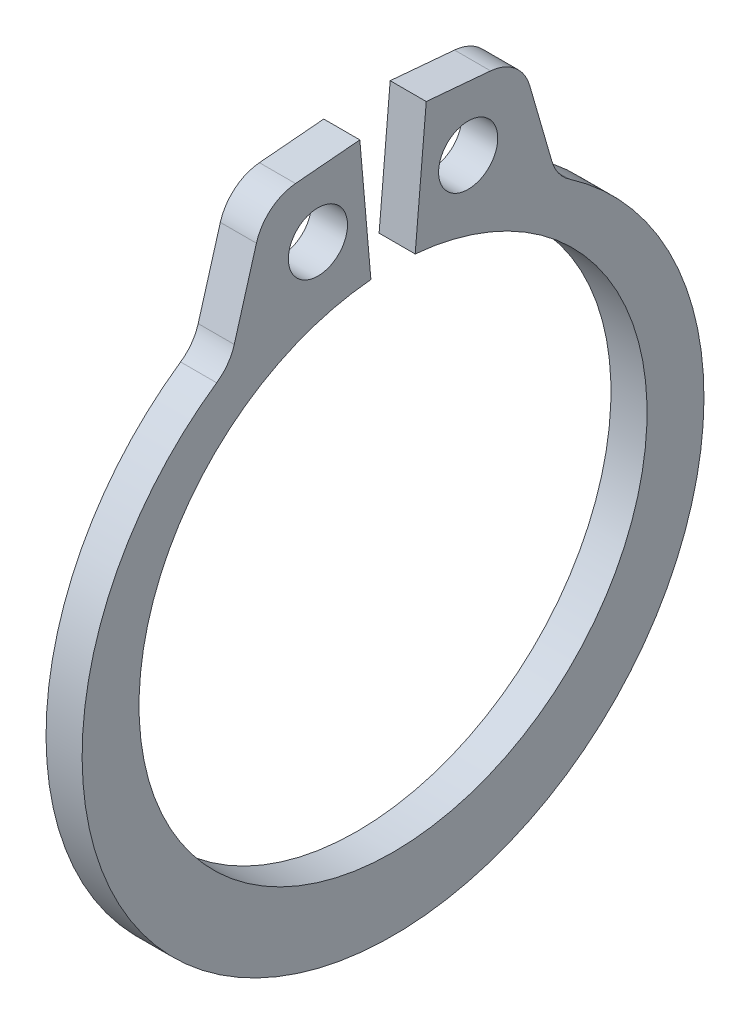
SolidWorks part; units mm, degrees
material "Cast Carbon Steel"
ref_plane "Front" through (0, 0, 0) normal (0, 0, 1) x (1, 0, 0)
ref_plane "Top" through (0, 0, 0) normal (0, 1, 0) x (1, 0, 0)
ref_plane "Right" through (0, 0, 0) normal (1, 0, 0) x (0, 0, -1)
sketch "Sketch1" plane through (0, 0, 0) normal (1, 0, 0) x (0, 0, -1)
  line L0 (0, 0) -> (0, 4.4704) construction
  line L1 (-0.3896, 4.4534) -> (-0.5844, 6.6801)
  line L2 (0.5844, 6.6801) -> (2.2545, 6.534)
  line L3 (2.2545, 6.534) -> (2.8753, 4.3867)
  line L4 (0.3896, 4.4534) -> (0.5844, 6.6801)
  line L5 (-0.5844, 6.6801) -> (-2.2545, 6.534)
  line L6 (-2.2545, 6.534) -> (-2.8753, 4.3867)
  line L7 (-2.8753, 4.3867) -> (-2.4507, 3.7388) construction
  line L8 (2.8753, 4.3867) -> (2.4507, 3.7388) construction
  line L9 (0, -4.4704) -> (0, -5.7404) construction
  line L10 (-2.2545, 6.534) -> (-0.3896, 4.4534) construction
  line L11 (0, 4.4704) -> (0, 6.7056) construction
  line L12 (-4.4704, 0) -> (4.4704, 0) construction
  circle A0 centre (0, 0) radius 4.4704 construction
  arc A1 (-0.3896, 4.4534) -> (0.3896, 4.4534) centre (0, 0) ccw
  circle A3 centre (0, 0) radius 7.493 construction
  circle A4 centre (-1.322, 5.4937) radius 0.5207
  circle A5 centre (1.322, 5.4937) radius 0.5207
  arc A6 (-2.8753, 4.3867) -> (2.8753, 4.3867) centre (0, -0.2686) ccw
  point P0 (0, -5.7404)
  dimension "A" = 8.9408
  dimension "D2" = 1.6764
  dimension "L" = 14.986
  dimension "Hole" = 1.0414
  dimension "Smin" = 0.7747
  dimension "Smax" = 1.27
  dimension "H" = 2.2352
  dimension "Angle" = 5
extrude "Extrude1" add sketch "Sketch1" along normal mid plane 0.635
fillet "Fillet1" radius 0.7874 4 edges at (0, 4.3867, 2.8753) (0, 4.3867, -2.8753) (0, 6.534, 2.2545) (0, 6.534, -2.2545)
sketch "Sketch2" plane through (0, 0, 0) normal (0, 0, 1) x (1, 0, 0)
  line L0 (-3.5433, 0) -> (9.1567, 0)
  line L1 (9.1567, 0) -> (9.1567, -4.7625)
  line L2 (-0.3683, -4.7625) -> (-3.2512, -4.7625)
  line L3 (9.1567, -4.7625) -> (0.3683, -4.7625)
  line L4 (0.3683, -4.7625) -> (0.3683, -4.4704)
  line L5 (0.3683, -4.4704) -> (-0.3683, -4.4704)
  line L6 (-0.3683, -4.4704) -> (-0.3683, -4.7625)
  line L7 (-0.3683, -4.7625) -> (-3.5433, -4.7625) construction
  line L8 (-3.5433, -4.7625) -> (-3.5433, 0) construction
  line L9 (9.1567, 0) -> (76.391, 0) construction
  line L10 (-3.2512, -4.7625) -> (-3.5433, -4.4704)
  line L11 (-3.5433, -4.4704) -> (-3.5433, 0)
  point P10 (0, -4.4704)
  dimension "D1" = 45
  dimension "Dg" = 8.9408
  dimension "Ds" = 9.525
  dimension "W" = 0.7366
  dimension "D2" = 12.7
  dimension "D3" = 3.175
revolve "Revolve1" [suppressed] add sketch "Sketch2" angle 360 about L9
delete or keep bodies "Body-Delete1" [suppressed] type delete bodies bodies 122
equation "\"D2@Sketch2\" = \"D1@Extrude1\"*20"
equation "\"D3@Sketch2\" = \"D2@Sketch2\"/4"
equation "\"D2@Sketch1\" = \"H@Sketch1\"*.75"
